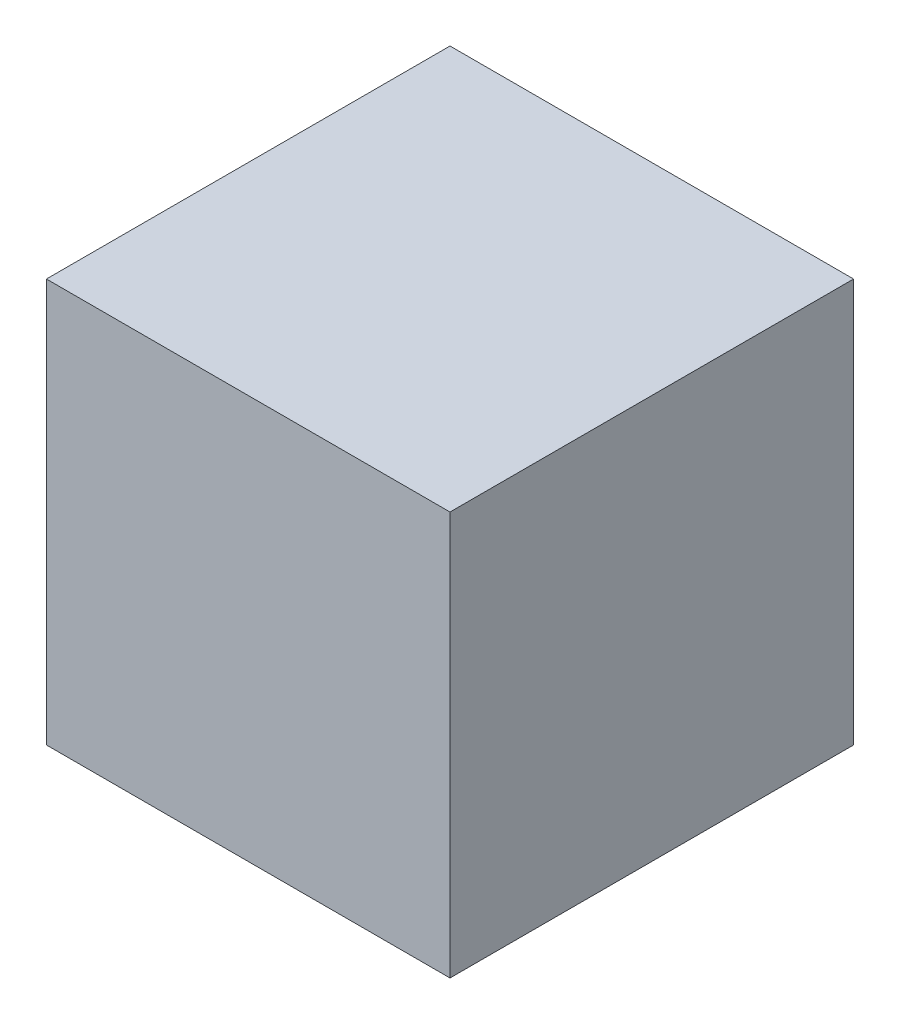
SolidWorks part; units mm, degrees
ref_plane "Front Plane" through (0, 0, 0) normal (0, 0, 1) x (1, 0, 0)
ref_plane "Top Plane" through (0, 0, 0) normal (0, 1, 0) x (1, 0, 0)
ref_plane "Right Plane" through (0, 0, 0) normal (1, 0, 0) x (0, 0, -1)
sketch "Sketch1" plane through (0, 0, 0) normal (0, 0, 1) x (1, 0, 0)
  line L1 (-150, 150) -> (150, 150)
  line L2 (-150, 150) -> (-150, -150)
  line L3 (-150, -150) -> (150, -150)
  line L4 (150, 150) -> (150, -150)
  line L5 (0, -150) -> (0, 150) construction
  line L6 (-150, 0) -> (150, 0) construction
  point P0 (0, 0)
  dimension "D1" = 300
  dimension "D2" = 300
extrude "Boss-Extrude1" add sketch "Sketch1" along normal blind 300
